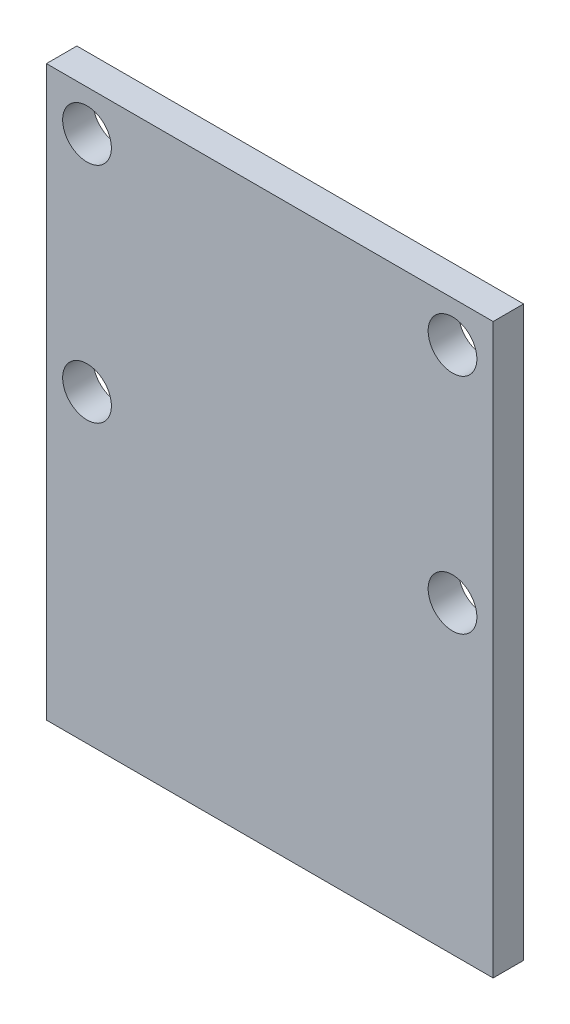
SolidWorks part; units mm, degrees
ref_plane "正面" through (0, 0, 0) normal (0, 0, 1) x (1, 0, 0)
ref_plane "平面" through (0, 0, 0) normal (0, 1, 0) x (1, 0, 0)
ref_plane "右側面" through (0, 0, 0) normal (1, 0, 0) x (0, 0, -1)
sketch "ｽｹｯﾁ1" plane through (0, 0, 0) normal (0, 0, 1) x (1, 0, 0)
  line L1 (-11, 14) -> (11, 14)
  line L2 (-11, 14) -> (-11, -14)
  line L3 (-11, -14) -> (11, -14)
  line L4 (11, 14) -> (11, -14)
  line L5 (-11, 14) -> (11, -14) construction
  line L6 (-11, -14) -> (11, 14) construction
  point P0 (0, 0)
  dimension "D1" = 22
  dimension "D2" = 28
extrude "ﾎﾞｽ - 押し出し1" add sketch "ｽｹｯﾁ1" along normal blind 1.5
sketch "ｽｹｯﾁ2" plane through (0, 0, 1.5) normal (0, 0, 1) x (1, 0, 0)
  line L0 (11, 14) -> (-11, 14) construction
  line L1 (-9, 12) -> (9, 12)
  line L2 (-9, 12) -> (-9, 1)
  line L3 (-9, 1) -> (9, 1)
  line L4 (9, 12) -> (9, 1)
  line L5 (-9, 12) -> (9, 1) construction
  line L6 (-9, 1) -> (9, 12) construction
  point P0 (0, 6.5)
  point P8 (0, 0)
  dimension "D1" = 2
  dimension "D2" = 11
  dimension "D3" = 18
hole_wizard "M2 すきま穴1" positions "ｽｹｯﾁ3" profile "ｽｹｯﾁ4" hole size "M2" standard "JIS" end condition through all
sketch "ｽｹｯﾁ3" plane through (0, 0, 1.5) normal (0, 0, 1) x (1, 0, 0)
  point P0 (-9, 12)
  point P3 (9, 12)
  point P6 (-9, 1)
  point P9 (9, 1)
sketch "ｽｹｯﾁ4" plane through (-9, 12, 1.5) normal (1, 0, 0) x (0, -1, 0)
  line L0 (0, 0) -> (0, 1.5)
  line L1 (0, 1.5) -> (1.2, 1.5)
  line L2 (1.2, 1.5) -> (1.2, 0)
  line L5 (1.2, 0) -> (0, 0)
  line L11 (0, -6.35) -> (0, 107.95) construction
  dimension "通し穴の直径" = 2.4
  dimension "通し穴の深さ" = 1.5
